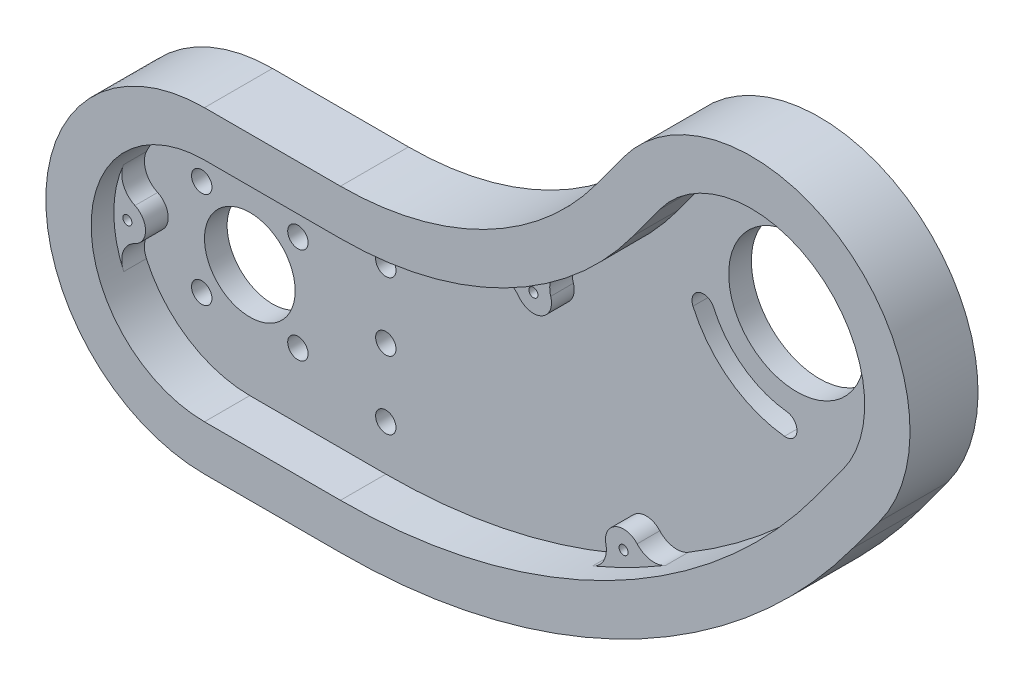
SolidWorks part; units mm, degrees
ref_plane "정면" through (0, 0, 0) normal (0, 0, 1) x (1, 0, 0)
ref_plane "윗면" through (0, 0, 0) normal (0, 1, 0) x (1, 0, 0)
ref_plane "우측면" through (0, 0, 0) normal (1, 0, 0) x (0, 0, -1)
sketch "스케치1" plane through (0, 0, 0) normal (0, 0, 1) x (1, 0, 0)
  line L0 (-1000, 0) -> (49000, 0) construction
  line L1 (0, -990) -> (0, -35) construction
  line L2 (-677.1068, -672.1068) -> (34678.2323, 34683.2323) construction
  line L3 (0, 35) -> (30, 35)
  line L5 (0, -35) -> (30, -35)
  line L8 (30, -955) -> (30, -35) construction
  line L10 (86.4793, 63.6467) -> (92.3869, 71.7152)
  line L11 (142.9585, 22.2935) -> (148.8662, 30.362)
  line L13 (0, 35) -> (0, 48990) construction
  line L14 (30, 35) -> (30, 49045) construction
  line L15 (121.3187, 16.0454) -> (142.9585, 22.2935)
  line L17 (92.3869, 71.7152) -> (148.8662, 30.362) construction
  arc A0 (0, 35) -> (0, -35) centre (0, 0) ccw
  arc A2 (30, 35) -> (86.4793, 63.6467) centre (30, 105) ccw
  arc A3 (30, -35) -> (142.9585, 22.2935) centre (30, 105) ccw
  arc A4 (121.3187, 16.0454) -> (122.5857, 16.0935) centre (120.6265, 51.0386) ccw
  arc A5 (148.8662, 30.362) -> (92.3869, 71.7152) centre (120.6265, 51.0386) ccw
  dimension "D1" = 70
  dimension "D2" = 70
  dimension "D3" = 30
  dimension "D6" = 140
  dimension "D7" = 70
  dimension "D8" = 35
  dimension "D4" = 10
  dimension "D5" = 70
extrude "보스-돌출1" add sketch "스케치1" along normal blind 20
chamfer "모따기1" distance 10 angle 45 8 edges at (141.3031, 79.2782, 20) (89.4331, 67.681, 20) (145.9123, 26.3277, 20) (61.6644, 42.5711, 20) (93.3289, -19.8577, 20) (15, 35, 20) (15, -35, 20) (-35, 0, 20)
sketch "스케치2" plane through (0, 0, 20) normal (0, 0, 1) x (1, 0, 0)
  line L8 (134.8901, 28.2011) -> (140.7977, 36.2696)
  line L10 (30, 25) -> (0, 25)
  line L11 (0, -25) -> (30, -25)
  line L14 (30, 25) -> (0, 25)
  line L15 (0, -25) -> (30, -25)
  line L20 (134.8901, 28.2011) -> (140.7977, 36.2696)
  line L22 (100.4553, 65.8076) -> (94.5477, 57.7391)
  line L23 (100.4553, 65.8076) -> (94.5477, 57.7391)
  arc A8 (140.7977, 36.2696) -> (100.4553, 65.8076) centre (120.6265, 51.0386) ccw
  arc A9 (30, 25) -> (94.5477, 57.7391) centre (30, 105) ccw
  arc A10 (0, 25) -> (0, -25) centre (0, 0) ccw
  arc A11 (30, -25) -> (134.8901, 28.2011) centre (30, 105) ccw
  arc A13 (30, 25) -> (94.5477, 57.7391) centre (30, 105) ccw
  arc A14 (0, 25) -> (0, -25) centre (0, 0) ccw
  arc A15 (30, -25) -> (134.8901, 28.2011) centre (30, 105) ccw
  arc A19 (140.7977, 36.2696) -> (100.4553, 65.8076) centre (120.6265, 51.0386) ccw
  dimension "D1" = 0
extrude "컷-돌출1" cut sketch "스케치2" against normal blind 15
sketch "스케치3" plane through (0, 0, 5) normal (0, 0, 1) x (1, 0, 0)
  circle A0 centre (120.6265, 51.0386) radius 15
  dimension "D1" = 30
extrude "컷-돌출2" cut sketch "스케치3" against normal blind 20
sketch "스케치4" plane through (0, 0, 5) normal (0, 0, 1) x (1, 0, 0)
  line L0 (0, -967.2447) -> (0, 49032.7553) construction
  line L1 (0, 0) -> (35355.3391, 35355.3391) construction
  line L2 (-1030, 0) -> (48970, 0) construction
  line L3 (30, -1000.0889) -> (30, 48999.9111) construction
  line L4 (0, 0) -> (35355.3391, -35355.3391) construction
  circle A0 centre (0, 0) radius 15
  circle A1 centre (10.6066, 10.6066) radius 2.25
  circle A2 centre (10.6066, -10.6066) radius 2.25
  circle A3 centre (-10.6066, -10.6066) radius 2.25
  circle A4 centre (-10.6066, 10.6066) radius 2.25
  circle A5 centre (30, 0) radius 2.25
  circle A6 centre (30, 15) radius 2.25
  circle A7 centre (30, -15) radius 2.25
  circle A8 centre (0, 0) radius 10
  arc A9 (0, 25) -> (0, -25) centre (0, 0) ccw construction
  point P14 (0, 0)
  point P27 (-25, 0)
  dimension "D1" = 4
  dimension "D2" = 30
  dimension "D3" = 15
  dimension "D8" = 4.5
  dimension "D9" = 4.5
  dimension "D10" = 4.5
  dimension "D11" = 4.5
  dimension "D4" = 15
  dimension "D5" = 30
  dimension "D6" = 45
  dimension "D7" = 45
extrude "컷-돌출3" cut sketch "스케치4" against normal blind 20 contours A0 A4 | A0 A4 | A1 | A3 | A2 | A6 | A5 | A7 | A8
sketch "스케치5" plane through (0, 0, 5) normal (0, 0, 1) x (1, 0, 0)
  line L0 (191.9651, 148.4711) -> (-25131.8533, -34438.1847) construction
  line L1 (30, -970) -> (30, 49030) construction
  line L2 (90.5975, 60.6314) -> (34677.2534, -25263.187) construction
  line L3 (-503.3048, 1156.4517) -> (20690.3128, -40628.4055) construction
  circle A0 centre (-22, 0) radius 4
  arc A1 (140.7977, 36.2696) -> (100.4553, 65.8076) centre (120.6265, 51.0386) ccw construction
  circle A2 centre (133.6233, 68.7892) radius 4
  arc A3 (30, 25) -> (94.5477, 57.7391) centre (30, 105) ccw construction
  arc A4 (30, -25) -> (134.8901, 28.2011) centre (30, 105) ccw construction
  circle A5 centre (67.545, 30.9772) radius 4
  circle A6 centre (87.4483, -8.2638) radius 4
  arc A7 (0, 25) -> (0, -25) centre (0, 0) ccw construction
  point P13 (135.3955, 71.2098)
  point P18 (30, 105)
  point P20 (66.1879, 33.6527)
  point P22 (88.8054, -10.9393)
  point P37 (-25, 0)
  dimension "D1" = 3
  dimension "D2" = 8
  dimension "D4" = 3
  dimension "D7" = 8
  dimension "D8" = 8
  dimension "D3" = 53.789
  dimension "D5" = 3
  dimension "D6" = 3
extrude "보스-돌출3" add sketch "스케치5" along normal blind 5
fillet "필렛1" radius 5 8 edges at (91.1801, -9.704, 7.5) (86.4057, -12.1255, 7.5) (133.0296, 72.7449, 7.5) (137.5735, 69.4179, 7.5) (68.4851, 34.8651, 7.5) (63.8526, 32.5155, 7.5) (-24.8409, -2.8159, 7.5) (-24.8409, 2.8159, 7.5)
sketch "스케치6" plane through (0, 0, 10) normal (0, 0, 1) x (1, 0, 0)
  circle A0 centre (67.545, 30.9772) radius 1
  circle A1 centre (87.4483, -8.2638) radius 1
  circle A2 centre (-22, 0) radius 1
  circle A3 centre (133.6233, 68.7892) radius 1
extrude "컷-돌출4" cut sketch "스케치6" against normal blind 10
fillet "필렛2" radius 5 8 edges at (15, 35, 10) (-35, 0, 10) (15, -35, 10) (93.3289, -19.8577, 10) (145.9123, 26.3277, 10) (141.3031, 79.2782, 10) (89.4331, 67.681, 10) (61.6644, 42.5711, 10)
sketch "스케치7" plane through (0, 0, 0) normal (0, 0, -1) x (-1, 0, 0)
  line L0 (493.7647, -788.082) -> (-108.8113, 34.9016) construction
  line L1 (-120.6265, 51.0386) -> (40221.7109, 29589.0787) construction
  line L4 (-120.6265, 51.0386) -> (-29658.6666, 40393.376) construction
  arc A0 (-117.9218, 26.1853) -> (-97.7506, 40.9543) centre (-120.6265, 51.0386) ccw
  arc A1 (-118.4627, 31.156) -> (-102.3258, 42.9712) centre (-120.6265, 51.0386) ccw
  arc A2 (-118.4627, 31.156) -> (-117.9218, 26.1853) centre (-118.1922, 28.6707) ccw
  arc A3 (-97.7506, 40.9543) -> (-102.3258, 42.9712) centre (-100.0382, 41.9628) ccw
  dimension "D1" = 50
  dimension "D2" = 40
  dimension "D3" = 5
  dimension "D4" = 5
  dimension "D5" = 22.5
  dimension "D6" = 22.5
extrude "컷-돌출5" cut sketch "스케치7" against normal up to next and the other way through all
ref_plane "평면1" through (0, 0, 20) normal (0, 0, -1) x (-1, 0, 0)
sketch "스케치8" plane through (0, 0, 20) normal (0, 0, -1) x (-1, 0, 0)
  line L20 (-30, -35) -> (0, -35)
  line L21 (-148.8662, 30.362) -> (-142.9585, 22.2935)
  line L22 (-86.4793, 63.6467) -> (-92.3869, 71.7152)
  line L23 (0, 35) -> (-30, 35)
  line L24 (-30, -35) -> (0, -35)
  line L25 (-148.8662, 30.362) -> (-142.9585, 22.2935)
  line L26 (-86.4793, 63.6467) -> (-92.3869, 71.7152)
  line L27 (0, 35) -> (-30, 35)
  line L50 (-30, -25) -> (0, -25)
  line L51 (-140.7977, 36.2696) -> (-134.8901, 28.2011)
  line L52 (-94.5477, 57.7391) -> (-100.4553, 65.8076)
  line L53 (0, 25) -> (-30, 25)
  line L54 (-30, -25) -> (0, -25)
  line L55 (-140.7977, 36.2696) -> (-134.8901, 28.2011)
  line L56 (-94.5477, 57.7391) -> (-100.4553, 65.8076)
  line L57 (0, 25) -> (-30, 25)
  arc A24 (-142.9585, 22.2935) -> (-30, -35) centre (-30, 105) ccw
  arc A25 (-92.3869, 71.7152) -> (-148.8662, 30.362) centre (-120.6265, 51.0386) ccw
  arc A26 (-86.4793, 63.6467) -> (-30, 35) centre (-30, 105) ccw
  arc A27 (0, -35) -> (0, 35) centre (0, 0) ccw
  arc A28 (-142.9585, 22.2935) -> (-30, -35) centre (-30, 105) ccw
  arc A29 (-92.3869, 71.7152) -> (-148.8662, 30.362) centre (-120.6265, 51.0386) ccw
  arc A30 (-86.4793, 63.6467) -> (-30, 35) centre (-30, 105) ccw
  arc A31 (0, -35) -> (0, 35) centre (0, 0) ccw
  arc A59 (-134.8901, 28.2011) -> (-30, -25) centre (-30, 105) ccw
  arc A60 (-100.4553, 65.8076) -> (-140.7977, 36.2696) centre (-120.6265, 51.0386) ccw
  arc A61 (-94.5477, 57.7391) -> (-30, 25) centre (-30, 105) ccw
  arc A62 (0, -25) -> (0, 25) centre (0, 0) ccw
  arc A63 (-134.8901, 28.2011) -> (-30, -25) centre (-30, 105) ccw
  arc A64 (-100.4553, 65.8076) -> (-140.7977, 36.2696) centre (-120.6265, 51.0386) ccw
  arc A65 (-94.5477, 57.7391) -> (-30, 25) centre (-30, 105) ccw
  arc A66 (0, -25) -> (0, 25) centre (0, 0) ccw
  dimension "D1" = 0
  dimension "D2" = 0
extrude "보스-돌출4" add sketch "스케치8" along normal blind 13
sketch "스케치9" plane through (0, 0, 20) normal (0, 0, 1) x (1, 0, 0)
  line L8 (0, -35) -> (30, -35)
  line L9 (142.9585, 22.2935) -> (148.8662, 30.362)
  line L10 (92.3869, 71.7152) -> (86.4793, 63.6467)
  line L11 (30, 35) -> (0, 35)
  line L12 (0, -35) -> (30, -35)
  line L13 (142.9585, 22.2935) -> (148.8662, 30.362)
  line L14 (92.3869, 71.7152) -> (86.4793, 63.6467)
  line L15 (30, 35) -> (0, 35)
  line L32 (0, -25) -> (30, -25)
  line L33 (134.8901, 28.2011) -> (140.7977, 36.2696)
  line L34 (100.4553, 65.8076) -> (94.5477, 57.7391)
  line L35 (30, 25) -> (0, 25)
  line L36 (0, -25) -> (30, -25)
  line L37 (134.8901, 28.2011) -> (140.7977, 36.2696)
  line L38 (100.4553, 65.8076) -> (94.5477, 57.7391)
  line L39 (30, 25) -> (0, 25)
  arc A8 (0, 35) -> (0, -35) centre (0, 0) ccw
  arc A9 (30, -35) -> (142.9585, 22.2935) centre (30, 105) ccw
  arc A10 (148.8662, 30.362) -> (92.3869, 71.7152) centre (120.6265, 51.0386) ccw
  arc A11 (30, 35) -> (86.4793, 63.6467) centre (30, 105) ccw
  arc A12 (0, 35) -> (0, -35) centre (0, 0) ccw
  arc A13 (30, -35) -> (142.9585, 22.2935) centre (30, 105) ccw
  arc A14 (148.8662, 30.362) -> (92.3869, 71.7152) centre (120.6265, 51.0386) ccw
  arc A15 (30, 35) -> (86.4793, 63.6467) centre (30, 105) ccw
  arc A36 (30, -25) -> (134.8901, 28.2011) centre (30, 105) ccw
  arc A37 (140.7977, 36.2696) -> (100.4553, 65.8076) centre (120.6265, 51.0386) ccw
  arc A38 (30, 25) -> (94.5477, 57.7391) centre (30, 105) ccw
  arc A39 (0, 25) -> (0, -25) centre (0, 0) ccw
  arc A40 (30, -25) -> (134.8901, 28.2011) centre (30, 105) ccw
  arc A41 (140.7977, 36.2696) -> (100.4553, 65.8076) centre (120.6265, 51.0386) ccw
  arc A42 (30, 25) -> (94.5477, 57.7391) centre (30, 105) ccw
  arc A43 (0, 25) -> (0, -25) centre (0, 0) ccw
  dimension "D1" = 0
  dimension "D2" = 0
extrude "컷-돌출6" cut sketch "스케치9" against normal blind 5
